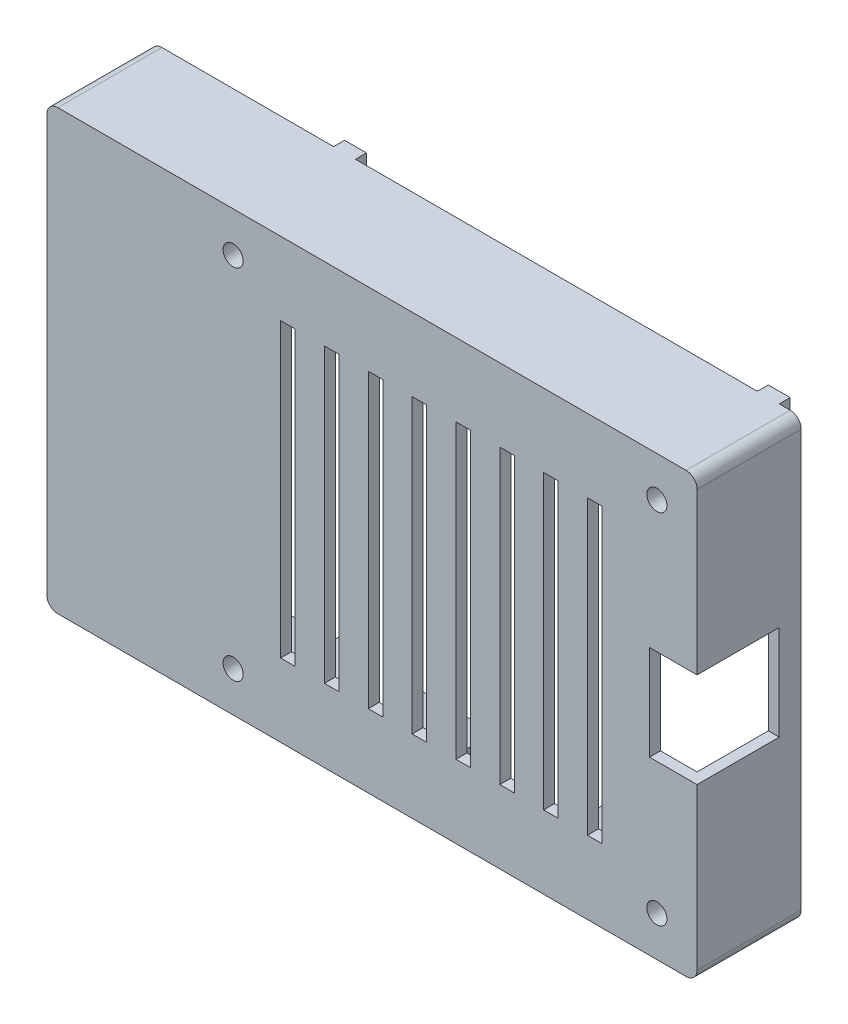
SolidWorks part; units mm, degrees
ref_plane "Front Plane" through (0, 0, 0) normal (0, 0, 1) x (1, 0, 0)
ref_plane "Top Plane" through (0, 0, 0) normal (0, 1, 0) x (1, 0, 0)
ref_plane "Right Plane" through (0, 0, 0) normal (1, 0, 0) x (0, 0, -1)
sketch "Sketch1" plane through (0, 0, 0) normal (0, 0, 1) x (1, 0, 0)
  line L1 (-81.5, 26.5) -> (-77.5, 26.5)
  line L2 (-81.5, 26.5) -> (-81.5, 22.5)
  line L3 (-81.5, 22.5) -> (-77.5, 22.5)
  line L4 (-77.5, 26.5) -> (-77.5, 22.5)
  line L5 (-81.5, -0.5) -> (-81.5, 49.5) construction
  circle A0 centre (0, 0) radius 3
  circle A1 centre (0, 49) radius 3
  circle A2 centre (-58, 0) radius 3
  circle A3 centre (-58, 49) radius 3
  point P18 (-81.5, 24.5)
  point P19 (-81.5, 24.5)
  dimension "D1" = 6
  dimension "D2" = 4
  dimension "D3" = 4
extrude "Boss-Extrude1" add sketch "Sketch1" along normal blind 2.5
sketch "Sketch2" plane through (0, 0, 2.5) normal (0, 0, 1) x (1, 0, 0)
  line L0 (3.5, 49.5) -> (3.5, -0.5) construction
  line L1 (5.5, -5.5) -> (-83.5, -5.5)
  line L2 (5.5, -5.5) -> (5.5, 54.5)
  line L3 (5.5, 54.5) -> (-83.5, 54.5)
  line L4 (-83.5, -5.5) -> (-83.5, 54.5)
  line L5 (0.5, -3.5) -> (-78.5, -3.5) construction
  line L6 (-78.5, 52.5) -> (0.5, 52.5) construction
  line L7 (-81.5, -0.5) -> (-81.5, 49.5) construction
  dimension "D1" = 2
  dimension "D2" = 2
  dimension "D3" = 2
  dimension "D4" = 2
extrude "Boss-Extrude2" add sketch "Sketch2" along normal blind 1.5
sketch "Sketch3" plane through (0, 0, 2.5) normal (0, 0, -1) x (-1, 0, 0)
  line L1 (-5.5, 54.5) -> (83.5, 54.5)
  line L2 (-5.5, 54.5) -> (-5.5, -5.5)
  line L3 (-5.5, -5.5) -> (83.5, -5.5)
  line L4 (83.5, 54.5) -> (83.5, -5.5)
  line L5 (-4, 53) -> (82, 53)
  line L6 (-4, 53) -> (-4, -4)
  line L7 (-4, -4) -> (82, -4)
  line L8 (82, 53) -> (82, -4)
  dimension "D1" = 1.5
  dimension "D2" = 1.5
  dimension "D3" = 1.5
  dimension "D4" = 1.5
extrude "Boss-Extrude3" add sketch "Sketch3" along normal offset from surface (12.75 mm away) 2.5
sketch "Sketch4" plane through (-83.5, 0, 0) normal (-1, 0, 0) x (0, 0, 1)
  line L0 (-10.25, -5.5) -> (-10.25, 54.5) construction
  line L1 (-10.25, 51.25) -> (-0.25, 51.25)
  line L2 (-10.25, 51.25) -> (-10.25, 35.75)
  line L3 (-10.25, 35.75) -> (-0.25, 35.75)
  line L4 (-0.25, 51.25) -> (-0.25, 35.75)
  line L5 (-14.25, 14.75) -> (-1.25, 14.75) construction
  line L6 (-10.25, 33.25) -> (-0.25, 33.25)
  line L7 (-10.25, 33.25) -> (-10.25, 17.75)
  line L8 (-10.25, 17.75) -> (-0.25, 17.75)
  line L9 (-0.25, 33.25) -> (-0.25, 17.75)
  line L10 (-10.25, 15.25) -> (-0.75, 15.25)
  line L11 (-10.25, 15.25) -> (-10.25, -1.75)
  line L12 (-10.25, -1.75) -> (-0.75, -1.75)
  line L13 (-0.75, 15.25) -> (-0.75, -1.75)
  line L14 (-14.25, -1.25) -> (-1.25, -1.25) construction
  line L15 (-1.25, -1.25) -> (-1.25, 14.75) construction
  line L16 (-16.25, 19) -> (-1.25, 19) construction
  line L17 (-1.25, 19) -> (-1.25, 32) construction
  line L18 (-16.25, 32) -> (-1.25, 32) construction
  line L19 (-16.25, 37) -> (-1.25, 37) construction
  line L20 (-1.25, 37) -> (-1.25, 50) construction
  line L21 (-16.25, 50) -> (-1.25, 50) construction
  dimension "D1" = 0.5
  dimension "D2" = 0.5
  dimension "D3" = 0.5
  dimension "D4" = 1.25
  dimension "D5" = 1
  dimension "D6" = 1.25
  dimension "D7" = 1.25
  dimension "D8" = 1
  dimension "D9" = 1.25
extrude "Cut-Extrude1" cut sketch "Sketch4" against normal up to next (1.5 mm away)
sketch "Sketch5" plane through (0, -5.5, 0) normal (0, -1, 0) x (1, 0, 0)
  line L0 (5.5, -10.25) -> (-83.5, -10.25) construction
  line L1 (-46.5, -10.25) -> (-53.5, -10.25)
  line L2 (-46.5, -10.25) -> (-46.5, -4.25)
  line L4 (-53.5, -10.25) -> (-53.5, -4.25)
  line L5 (-3.35, -1.25) -> (-10.85, -1.25) construction
  line L6 (-20.5, -10.25) -> (-36.5, -10.25)
  line L7 (-20.5, -10.25) -> (-20.5, -1.75)
  line L8 (-20.5, -1.75) -> (-36.5, -1.75)
  line L9 (-36.5, -10.25) -> (-36.5, -1.75)
  line L10 (-2.6, -10.25) -> (-11.6, -10.25)
  line L11 (-2.6, -10.25) -> (-2.6, -0.75)
  line L12 (-2.6, -0.75) -> (-11.6, -0.75)
  line L13 (-11.6, -10.25) -> (-11.6, -0.75)
  line L14 (-10.85, -3.75) -> (-10.85, -1.25) construction
  line L15 (-3.35, -3.75) -> (-3.35, -1.25) construction
  line L16 (-36, -4.25) -> (-36, -7.25) construction
  line L17 (-21, -7.25) -> (-21, -4.25) construction
  line L18 (-23.5, -2.25) -> (-33.5, -2.25) construction
  arc A0 (-46.5, -4.25) -> (-53.5, -4.25) centre (-50, -4.25) ccw
  circle A1 centre (-50, -4.25) radius 3 construction
  dimension "D7" = 0.5
  dimension "D1" = 0.5
  dimension "D2" = 0.75
  dimension "D3" = 0.75
  dimension "D4" = 0.5
  dimension "D5" = 0.5
  dimension "D6" = 0.5
extrude "Cut-Extrude2" cut sketch "Sketch5" against normal up to next (1.5 mm away)
sketch "Sketch6" plane through (5.5, 0, 0) normal (1, 0, 0) x (0, 0, -1)
  line L1 (7.25, 31) -> (-4, 31)
  line L2 (7.25, 31) -> (7.25, 18)
  line L3 (7.25, 18) -> (-4, 18)
  line L4 (-4, 31) -> (-4, 18)
  line L5 (10.25, 54.5) -> (10.25, -5.5) construction
  line L6 (-1.25, 30.5) -> (0, 30.5) construction
  line L7 (-1.25, 18.5) -> (0, 18.5) construction
  line L8 (-4, -5.5) -> (-4, 54.5) construction
  dimension "D1" = 3
  dimension "D2" = 0.5
  dimension "D3" = 0.5
extrude "Cut-Extrude3" cut sketch "Sketch6" against normal offset from surface (6.5 mm away) 5 up to face at (4, 24.5, -3.875) offset beyond the face yes
sketch "Sketch7" plane through (0, 0, 0) normal (0, 0, -1) x (-1, 0, 0)
  circle A0 centre (0, 0) radius 1.375
  circle A2 centre (0, 0) radius 1.375 construction
  circle A3 centre (0, 49) radius 1.375
  circle A4 centre (0, 49) radius 1.375 construction
  circle A5 centre (58, 49) radius 1.375
  circle A6 centre (58, 49) radius 1.375 construction
  circle A7 centre (58, 0) radius 1.375
  circle A8 centre (58, 0) radius 1.375 construction
extrude "Cut-Extrude4" cut sketch "Sketch7" against normal through all
sketch "Sketch10" plane through (0, 0, 4) normal (0, 0, 1) x (1, 0, 0)
  line L1 (-7.5, 4.5) -> (-9.5, 4.5)
  line L2 (-7.5, 4.5) -> (-7.5, 44.5)
  line L3 (-7.5, 44.5) -> (-9.5, 44.5)
  line L4 (-9.5, 4.5) -> (-9.5, 44.5)
  line L5 (-83.5, -5.5) -> (5.5, -5.5) construction
  line L6 (5.5, 31) -> (5.5, 54.5) construction
  line L7 (-13.5, 4.5) -> (-13.5, 44.5)
  line L8 (-15.5, 4.5) -> (-15.5, 44.5)
  line L9 (-13.5, 44.5) -> (-15.5, 44.5)
  line L10 (-13.5, 4.5) -> (-15.5, 4.5)
  line L11 (-19.5, 4.5) -> (-19.5, 44.5)
  line L12 (-21.5, 4.5) -> (-21.5, 44.5)
  line L13 (-19.5, 44.5) -> (-21.5, 44.5)
  line L14 (-19.5, 4.5) -> (-21.5, 4.5)
  line L15 (-25.5, 4.5) -> (-25.5, 44.5)
  line L16 (-27.5, 4.5) -> (-27.5, 44.5)
  line L17 (-25.5, 44.5) -> (-27.5, 44.5)
  line L18 (-25.5, 4.5) -> (-27.5, 4.5)
  line L19 (-31.5, 4.5) -> (-31.5, 44.5)
  line L20 (-33.5, 4.5) -> (-33.5, 44.5)
  line L21 (-31.5, 44.5) -> (-33.5, 44.5)
  line L22 (-31.5, 4.5) -> (-33.5, 4.5)
  line L23 (-37.5, 4.5) -> (-37.5, 44.5)
  line L24 (-39.5, 4.5) -> (-39.5, 44.5)
  line L25 (-37.5, 44.5) -> (-39.5, 44.5)
  line L26 (-37.5, 4.5) -> (-39.5, 4.5)
  line L27 (-43.5, 4.5) -> (-43.5, 44.5)
  line L28 (-45.5, 4.5) -> (-45.5, 44.5)
  line L29 (-43.5, 44.5) -> (-45.5, 44.5)
  line L30 (-43.5, 4.5) -> (-45.5, 4.5)
  line L31 (-49.5, 4.5) -> (-49.5, 44.5)
  line L32 (-51.5, 4.5) -> (-51.5, 44.5)
  line L33 (-49.5, 44.5) -> (-51.5, 44.5)
  line L34 (-49.5, 4.5) -> (-51.5, 4.5)
  dimension "D1" = 40
  dimension "D2" = 10
  dimension "D3" = 13
  dimension "D4" = 2
  dimension "D5" = 8
extrude "Cut-Extrude7" cut sketch "Sketch10" against normal through all
fillet "Fillet2" radius 1.5 4 edges at (-83.5, -5.5, -3.125) (5.5, -5.5, -3.125) (5.5, 54.5, -3.125) (-83.5, 54.5, -3.125)
sketch "Sketch12" plane through (0, 0, -10.25) normal (0, 0, -1) x (-1, 0, 0)
  line L0 (82, 53) -> (-4, 53) construction
  line L1 (-2.5, 53) -> (0.5, 53)
  line L2 (-2.5, 53) -> (-2.5, 54.5)
  line L3 (-2.5, 54.5) -> (0.5, 54.5)
  line L4 (0.5, 53) -> (0.5, 54.5)
  line L5 (82, 54.5) -> (-4, 54.5) construction
  line L6 (53.5, -5.5) -> (82, -5.5) construction
  line L7 (55.5, 53) -> (58.5, 53)
  line L8 (55.5, 53) -> (55.5, 54.5)
  line L9 (55.5, 54.5) -> (58.5, 54.5)
  line L10 (58.5, 53) -> (58.5, 54.5)
  line L11 (55.5, -5.5) -> (58.5, -5.5)
  line L12 (55.5, -5.5) -> (55.5, -4)
  line L13 (55.5, -4) -> (58.5, -4)
  line L14 (58.5, -5.5) -> (58.5, -4)
  line L15 (53.5, -4) -> (82, -4) construction
  line L16 (-4, -5.5) -> (2.6, -5.5) construction
  line L17 (-2.5, -5.5) -> (0.5, -5.5)
  line L18 (-2.5, -5.5) -> (-2.5, -4)
  line L19 (-2.5, -4) -> (0.5, -4)
  line L20 (0.5, -5.5) -> (0.5, -4)
  line L21 (-2.5, -4) -> (-2.5, 53) construction
  line L22 (58.5, 53) -> (58.5, -4) construction
  line L23 (83.5, -4) -> (83.5, -1.75) construction
  line L24 (-5.5, 53) -> (-5.5, -4) construction
  line L26 (-4, -4) -> (2.6, -4) construction
  dimension "D1" = 3
  dimension "D2" = 25
  dimension "D3" = 3
extrude "Boss-Extrude4" add sketch "Sketch12" along normal blind 1.5
